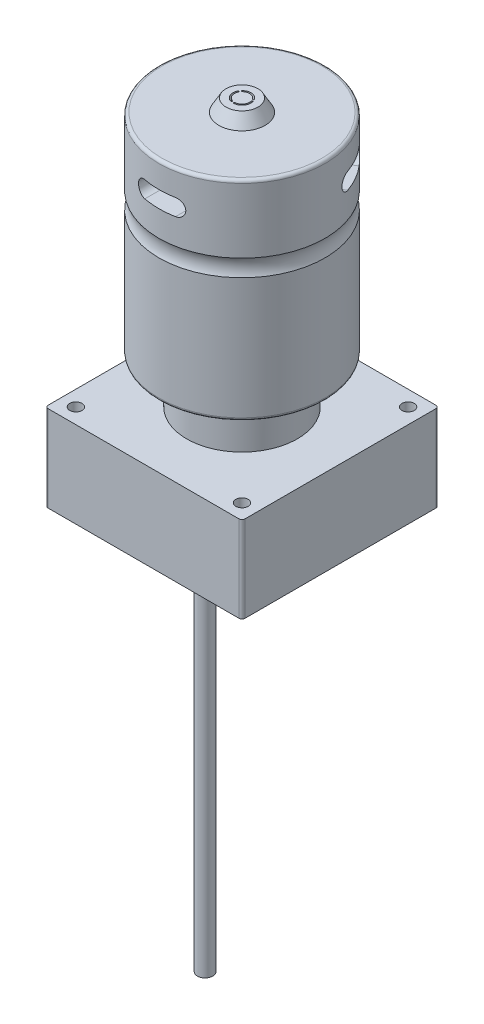
SolidWorks part; units mm, degrees
ref_plane "Front Plane" through (0, 0, 0) normal (0, 0, 1) x (1, 0, 0)
ref_plane "Top Plane" through (0, 0, 0) normal (0, 1, 0) x (1, 0, 0)
ref_plane "Right Plane" through (0, 0, 0) normal (1, 0, 0) x (0, 0, -1)
sketch "Sketch1" plane through (0, 0, 0) normal (0, 1, 0) x (1, 0, 0)
  line L0 (-32, 32) -> (32, -32) construction
  line L1 (-31, 32) -> (31, 32)
  line L2 (-32, 31) -> (-32, -31)
  line L3 (-31, -32) -> (31, -32)
  line L4 (32, 31) -> (32, -31)
  arc A0 (-31, -32) -> (-32, -31) centre (-31, -31) cw
  arc A1 (32, -31) -> (31, -32) centre (31, -31) cw
  arc A2 (32, 31) -> (31, 32) centre (31, 31) ccw
  arc A3 (-32, 31) -> (-31, 32) centre (-31, 31) cw
  dimension "D1" = 1
extrude "Boss-Extrude1" add sketch "Sketch1" along normal blind 28
sketch "Sketch2" plane through (0, 28, 0) normal (0, 1, 0) x (1, 0, 0)
  circle A0 centre (0, 0) radius 18
extrude "Boss-Extrude2" add sketch "Sketch2" along normal blind 15
sketch "Sketch3" plane through (0, 43, 0) normal (0, 1, 0) x (1, 0, 0)
  circle A0 centre (0, 0) radius 27
extrude "Boss-Extrude3" add sketch "Sketch3" along normal blind 68
fillet "Fillet1" radius 1 1 edges at (0, 43, 27)
fillet "Fillet2" radius 1 1 edges at (0, 111, 27)
sketch "Sketch4" plane through (0, 28, 0) normal (0, 1, 0) x (1, 0, 0)
  line L0 (-27, 27) -> (27, -27) construction
  line L1 (-27, 27) -> (27, 27) construction
  line L2 (-27, 27) -> (-27, -27) construction
  line L3 (-27, -27) -> (27, -27) construction
  line L4 (27, 27) -> (27, -27) construction
  circle A0 centre (-27, 27) radius 2
  circle A1 centre (27, 27) radius 2
  circle A2 centre (27, -27) radius 2
  circle A3 centre (-27, -27) radius 2
  point P15 (0, 0)
  dimension "D1" = 4
extrude "Cut-Extrude1" cut sketch "Sketch4" against normal through all
sketch "Sketch5" plane through (0, 0, 0) normal (0, -1, 0) x (1, 0, 0)
  line L0 (0, 32) -> (0, 12) construction
  line L1 (-31, 32) -> (31, 32) construction
  circle A0 centre (0, 12) radius 2.5
extrude "Boss-Extrude4" add sketch "Sketch5" along normal blind 125
sketch "Sketch6" plane through (0, 0, 0) normal (1, 0, 0) x (0, 0, -1)
  line L0 (27, 88.9423) -> (27, 83.4465)
  line L1 (27, 44) -> (27, 110) construction
  line L3 (27, 44) -> (27, 110) construction
  arc A0 (27, 83.4465) -> (27, 88.9423) centre (32.693, 86.1944) cw
revolve "Cut-Revolve1" cut sketch "Sketch6" angle 360 about axis through (0, 111, 0) along (0, -1, 0)
sketch "Sketch7" plane through (0, 111, 0) normal (0, 1, 0) x (1, 0, 0)
  circle A0 centre (0, 0) radius 7.5
extrude "Boss-Extrude5" add sketch "Sketch7" along normal blind 4 draft 30
ref_plane "Plane1" through (0, 0, 30) normal (0, 0, 1) x (1, 0, 0)
sketch "Sketch8" plane through (0, 0, 30) normal (0, 0, 1) x (1, 0, 0)
  line L0 (-5.066, 100) -> (4.934, 100) construction
  line L1 (-5.066, 102.6942) -> (4.934, 102.6942)
  line L2 (-5.066, 97.3058) -> (4.934, 97.3058)
  line L3 (-27, 110) -> (27, 110) construction
  arc A0 (-5.066, 102.6942) -> (-5.066, 97.3058) centre (-5.066, 100) ccw
  arc A1 (4.934, 97.3058) -> (4.934, 102.6942) centre (4.934, 100) ccw
  point P2 (-0.066, 100)
  dimension "D1" = 10
  dimension "D2" = 10
extrude "Cut-Extrude2" cut sketch "Sketch8" against normal blind 10
pattern_circular "CirPattern1" count 3 over 360 about axis through (0, 0, 0) along (0, 1, 0) of "Cut-Extrude2"
sketch "Sketch9" plane through (0, 115, 0) normal (0, 1, 0) x (1, 0, 0)
  arc A0 (2.239, 1.4939) -> (-1.86, 1.9455) centre (0, 0) ccw construction
  arc A1 (2.4248, 1.6179) -> (-2.0144, 2.107) centre (0, 0) ccw
  arc A2 (2.0531, 1.3699) -> (-1.7056, 1.784) centre (0, 0) ccw
  arc A3 (2.0531, 1.3699) -> (2.4248, 1.6179) centre (2.239, 1.4939) ccw
  arc A4 (-2.0144, 2.107) -> (-1.7056, 1.784) centre (-1.86, 1.9455) ccw
  point P4 (0.2948, 2.6754)
  dimension "D1" = 100
extrude "Cut-Extrude3" cut sketch "Sketch9" against normal blind 10
pattern_circular "CirPattern2" count 3 over 360 about axis through (0, 0, 0) along (0, 1, 0) of "Cut-Extrude3"
